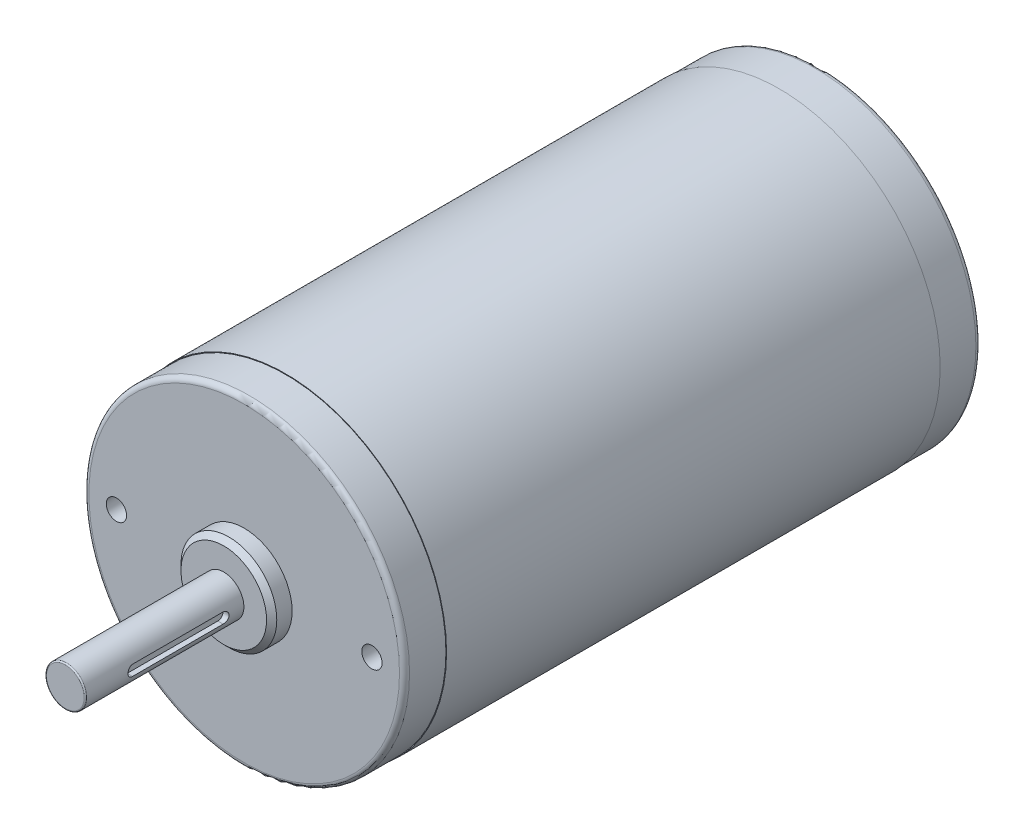
SolidWorks part; units mm, degrees
ref_plane "Front Plane" through (0, 0, 0) normal (0, 0, 1) x (1, 0, 0)
ref_plane "Top Plane" through (0, 0, 0) normal (0, 1, 0) x (1, 0, 0)
ref_plane "Right Plane" through (0, 0, 0) normal (1, 0, 0) x (0, 0, -1)
ref_plane "Plane1" through (0, 109.2962, 0) normal (0, -1, 0) x (1, 0, 0)
sketch "Sketch1" plane through (0, 109.2962, 0) normal (0, -1, 0) x (1, 0, 0)
  line L0 (67.564, 10.8204) -> (35.56, 10.8204)
  line L1 (35.56, 10.8204) -> (35.56, -87.3252)
  line L2 (35.56, -87.3252) -> (67.564, -87.3252)
  line L3 (67.564, -87.3252) -> (67.564, 10.8204)
  line L4 (35.56, 10.8204) -> (35.56, -87.3252) construction
revolve "Revolve1" add sketch "Sketch1" angle 360 about L4
sketch "Sketch2" plane through (0, 0, -87.3252) normal (0, 0, -1) x (-1, 0, 0)
  circle A0 centre (-35.56, 109.2962) radius 31.877
extrude "Boss-Extrude1" add sketch "Sketch2" along normal blind 8.2296
sketch "Sketch3" plane through (0, 0, -95.5548) normal (0, 0, -1) x (-1, 0, 0)
  circle A0 centre (-35.56, 109.2962) radius 15.0368
extrude "Boss-Extrude2" add sketch "Sketch3" along normal blind 4.7625
sketch "Sketch4" plane through (0, 0, 10.8204) normal (0, 0, 1) x (1, 0, 0)
  circle A0 centre (35.56, 109.2962) radius 31.877
extrude "Boss-Extrude3" add sketch "Sketch4" along normal blind 8.2296
sketch "Sketch5" plane through (0, 0, 19.05) normal (0, 0, 1) x (1, 0, 0)
  circle A0 centre (35.56, 109.2962) radius 9.525
extrude "Boss-Extrude4" add sketch "Sketch5" along normal blind 4.064
sketch "Sketch6" plane through (0, 0, 23.114) normal (0, 0, 1) x (1, 0, 0)
  circle A0 centre (35.56, 109.2962) radius 4
extrude "Boss-Extrude5" add sketch "Sketch6" along normal blind 31.5
imported_body "Surface-Imported1"
ref_plane "Plane2" through (38.36, 0, 0) normal (-1, 0, 0) x (0, -1, 0)
sketch "Sketch7" plane through (38.36, 0, 0) normal (-1, 0, 0) x (0, -1, 0)
  line L0 (-108.2462, 27.1) -> (-108.2462, 45.1)
  line L1 (-110.3462, 45.1) -> (-110.3462, 27.1)
  arc A0 (-108.2462, 45.1) -> (-110.3462, 45.1) centre (-109.2962, 45.1) ccw
  arc A1 (-110.3462, 27.1) -> (-108.2462, 27.1) centre (-109.2962, 27.1) ccw
extrude "Cut-Extrude1" cut sketch "Sketch7" against normal up to surface
ref_plane "Plane3" through (0, 120.5036, 0) normal (0, -1, 0) x (1, 0, 0)
sketch "Sketch8" plane through (0, 120.5036, 0) normal (0, -1, 0) x (1, 0, 0)
  line L0 (58.4851, -95.5548) -> (54.1671, -95.5548)
  line L1 (54.1671, -95.5548) -> (54.1671, -97.8027)
  line L2 (54.1671, -97.8027) -> (56.2851, -97.8027)
  line L3 (56.2851, -97.8027) -> (58.4851, -95.6027)
  line L4 (58.4851, -95.6027) -> (58.4851, -95.5548)
  line L5 (54.1671, -95.5548) -> (54.1671, -97.8027) construction
revolve "Revolve2" add sketch "Sketch8" angle 360 about L5
ref_plane "Plane4" through (0, 127.9033, 0) normal (0, -1, 0) x (1, 0, 0)
sketch "Sketch9" plane through (0, 127.9033, 0) normal (0, -1, 0) x (1, 0, 0)
  line L0 (51.0854, -95.5548) -> (46.7674, -95.5548)
  line L1 (46.7674, -95.5548) -> (46.7674, -97.8027)
  line L2 (46.7674, -97.8027) -> (48.8854, -97.8027)
  line L3 (48.8854, -97.8027) -> (51.0854, -95.6027)
  line L4 (51.0854, -95.6027) -> (51.0854, -95.5548)
  line L5 (46.7674, -95.5548) -> (46.7674, -97.8027) construction
revolve "Revolve3" add sketch "Sketch9" angle 360 about L5
hole_wizard "#21 (0.159) Diameter Hole1" positions "Sketch11" profile "Sketch10" hole size "#21" standard "ANSI Inch"
sketch "Sketch11" plane through (0, 0, 19.05) normal (0, 0, 1) x (1, 0, 0)
  point P0 (10.16, 109.2962)
  point P1 (60.96, 109.2962)
sketch "Sketch10" plane through (10.16, 109.2962, 19.05) normal (1, 0, 0) x (0, -1, 0)
  line L0 (0, 0) -> (0, 14.8277)
  line L1 (0, 14.8277) -> (2.0193, 13.6144)
  line L2 (2.0193, 13.6144) -> (2.0193, 0)
  line L5 (2.0193, 0) -> (0, 0)
  line L10 (0, 14.8277) -> (-2.0193, 13.6144) construction
  line L11 (0, -6.35) -> (0, 107.95) construction
  dimension "Hole Dia." = 4.0386
  dimension "Hole Depth" = 13.6144
  dimension "Drill Angle" = 118
chamfer "Chamfer1" distance 1.016 angle 45 1 edges at (45.085, 109.2962, 23.114)
fillet "Fillet1" radius 0.254 1 edges at (39.56, 109.2962, 54.614)
fillet "Fillet2" radius 1 3 edges at (67.437, 109.2962, 19.05) (3.683, 109.2962, -95.5548) (20.5232, 109.2962, -100.3173)
